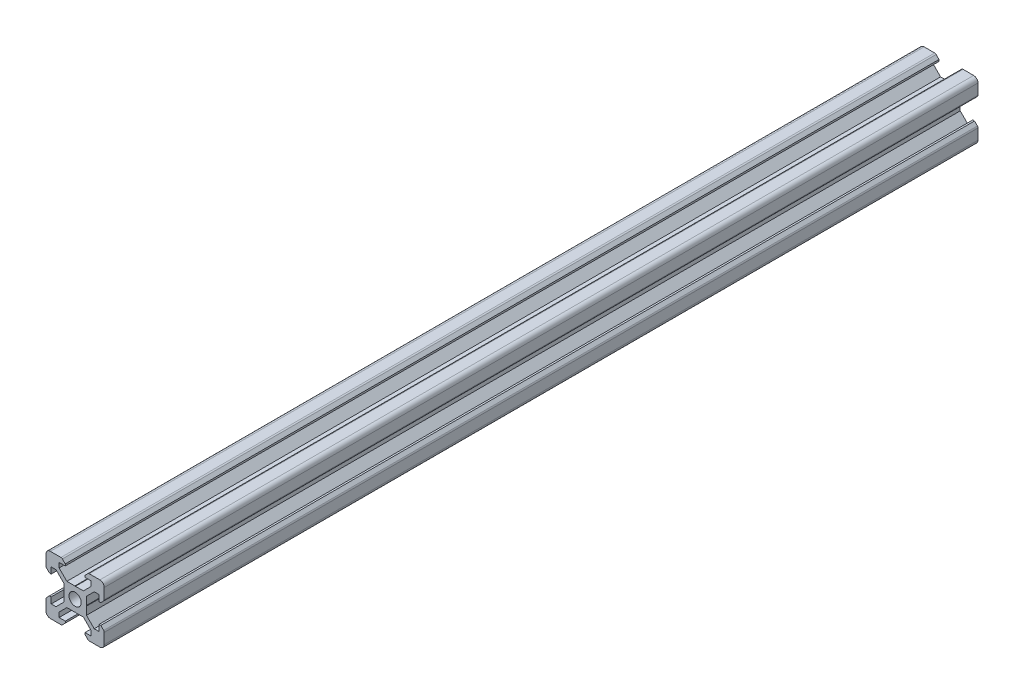
SolidWorks part; units mm, degrees
ref_plane "Front" through (0, 0, 0) normal (0, 0, 1) x (1, 0, 0)
ref_plane "Top" through (0, 0, 0) normal (0, 1, 0) x (1, 0, 0)
ref_plane "Right" through (0, 0, 0) normal (1, 0, 0) x (0, 0, -1)
sketch "Sketch1" plane through (0, 0, 0) normal (0, 0, 1) x (1, 0, 0)
  line L0 (-8.5, 10) -> (-10, 8.5) construction
  line L1 (-8.5, 10) -> (-4.8628, 10)
  line L2 (-10, 8.5) -> (-10, 4.8628)
  line L3 (-8.5, -10) -> (-4.8628, -10)
  line L4 (10, 8.5) -> (10, 4.8628)
  line L5 (-10, 10) -> (10, -10) construction
  line L6 (-10, -10) -> (10, 10) construction
  line L7 (-5.5, -8.2) -> (-3.3865, -8.2)
  line L8 (-8.2, -5.5) -> (-8.2, -3.3865)
  line L9 (-5.5, 8.2) -> (-3.3865, 8.2)
  line L10 (8.2, -5.5) -> (8.2, -3.3865)
  line L11 (-3.9005, 2.8395) -> (-6.561, 5.5)
  line L12 (-6.561, 5.5) -> (-8.2, 5.5)
  line L13 (-2.8395, -3.9005) -> (-0.1, -3.9005)
  line L14 (-3.9005, -2.8395) -> (-3.9005, -0.1)
  line L15 (-2.8395, 3.9005) -> (-0.1, 3.9005)
  line L16 (3.9005, -2.8395) -> (3.9005, -0.1)
  line L17 (-8.2, 3.3865) -> (-8.81, 3.3865)
  line L18 (-8.81, 3.3865) -> (-9.7976, 4.3741)
  line L19 (8.5, 10) -> (10, 8.5) construction
  line L20 (-2.8395, 3.9005) -> (-5.5, 6.561)
  line L21 (-5.5, 6.561) -> (-5.5, 8.2)
  line L22 (-3.3865, 8.2) -> (-3.3865, 8.81)
  line L23 (-3.3865, 8.81) -> (-4.3741, 9.7976)
  line L24 (0, 24.069) -> (0, -33.8154) construction
  line L25 (3.3865, 8.81) -> (4.3741, 9.7976)
  line L26 (3.3865, 8.2) -> (3.3865, 8.81)
  line L27 (5.5, 6.561) -> (5.5, 8.2)
  line L28 (2.8395, 3.9005) -> (5.5, 6.561)
  line L29 (3.3865, 8.2) -> (5.5, 8.2)
  line L30 (4.8628, 10) -> (8.5, 10)
  line L31 (-0.1, 3.9005) -> (0, 3.8005)
  line L32 (0.1, 3.9005) -> (0, 3.8005)
  line L33 (0.1, 3.9005) -> (2.8395, 3.9005)
  line L34 (25.9287, 0) -> (-28.3459, 0) construction
  line L35 (-0.1, -3.9005) -> (0, -3.8005)
  line L36 (0.1, -3.9005) -> (0, -3.8005)
  line L37 (0.1, -3.9005) -> (2.8395, -3.9005)
  line L38 (-3.9005, 0.1) -> (-3.8005, 0)
  line L39 (-3.8005, 0) -> (-3.9005, -0.1)
  line L40 (-3.9005, 0.1) -> (-3.9005, 2.8395)
  line L41 (3.9005, 0.1) -> (3.8005, 0)
  line L42 (3.8005, 0) -> (3.9005, -0.1)
  line L43 (3.9005, 0.1) -> (3.9005, 2.8395)
  line L44 (8.81, 3.3865) -> (9.7976, 4.3741)
  line L45 (8.2, 3.3865) -> (8.81, 3.3865)
  line L46 (6.561, 5.5) -> (8.2, 5.5)
  line L47 (3.9005, 2.8395) -> (6.561, 5.5)
  line L48 (2.8395, -3.9005) -> (5.5, -6.561)
  line L49 (3.9005, -2.8395) -> (6.561, -5.5)
  line L50 (-2.8395, -3.9005) -> (-5.5, -6.561)
  line L51 (-3.9005, -2.8395) -> (-6.561, -5.5)
  line L52 (6.561, -5.5) -> (8.2, -5.5)
  line L53 (-6.561, -5.5) -> (-8.2, -5.5)
  line L54 (-8.81, -3.3865) -> (-9.7976, -4.3741)
  line L55 (-8.2, -3.3865) -> (-8.81, -3.3865)
  line L56 (8.81, -3.3865) -> (9.7976, -4.3741)
  line L57 (8.2, -3.3865) -> (8.81, -3.3865)
  line L58 (8.2, 3.3865) -> (8.2, 5.5)
  line L59 (10, -4.8628) -> (10, -8.5)
  line L60 (-8.2, 3.3865) -> (-8.2, 5.5)
  line L61 (-10, -4.8628) -> (-10, -8.5)
  line L62 (-3.3865, -8.81) -> (-4.3741, -9.7976)
  line L63 (-3.3865, -8.2) -> (-3.3865, -8.81)
  line L64 (3.3865, -8.81) -> (4.3741, -9.7976)
  line L65 (3.3865, -8.2) -> (3.3865, -8.81)
  line L66 (-5.5, -6.561) -> (-5.5, -8.2)
  line L67 (5.5, -6.561) -> (5.5, -8.2)
  line L68 (3.3865, -8.2) -> (5.5, -8.2)
  line L69 (4.8628, -10) -> (8.5, -10)
  circle A0 centre (0, 0) radius 2.1
  arc A1 (-8.5, 10) -> (-10, 8.5) centre (-8.5, 8.5) ccw
  arc A2 (10, 8.5) -> (8.5, 10) centre (8.5, 8.5) ccw
  arc A3 (-4.3741, 9.7976) -> (-4.8628, 10) centre (-4.8628, 9.3088) ccw
  arc A4 (4.8628, 10) -> (4.3741, 9.7976) centre (4.8628, 9.3088) ccw
  arc A5 (-8.5, -10) -> (-10, -8.5) centre (-8.5, -8.5) cw
  arc A6 (9.7976, 4.3741) -> (10, 4.8628) centre (9.3088, 4.8628) ccw
  arc A7 (-10, 4.8628) -> (-9.7976, 4.3741) centre (-9.3088, 4.8628) ccw
  arc A8 (-10, -4.8628) -> (-9.7976, -4.3741) centre (-9.3088, -4.8628) cw
  arc A9 (9.7976, -4.3741) -> (10, -4.8628) centre (9.3088, -4.8628) cw
  arc A10 (10, -8.5) -> (8.5, -10) centre (8.5, -8.5) cw
  arc A11 (-4.3741, -9.7976) -> (-4.8628, -10) centre (-4.8628, -9.3088) cw
  arc A12 (4.8628, -10) -> (4.3741, -9.7976) centre (4.8628, -9.3088) cw
  point P17 (-9.25, 9.25)
  point P21 (9.25, 9.25)
  dimension "D2" = 4.2
  dimension "D4" = 1.5
  dimension "D3" = 20
  dimension "D5" = 0.529
  dimension "D6" = 6.773
  dimension "D7" = 90
  dimension "D8" = 11
  dimension "D9" = 0.61
  dimension "D10" = 0.1
  dimension "D11" = 0.1
  dimension "D12" = 0.1
  dimension "D13" = 0.1
  dimension "D14" = 5.679
  dimension "D15" = 1.639
  dimension "D16" = 1.8
  dimension "D17" = 90
  dimension "D18" = 6.773
  dimension "D19" = 90
extrude "Boss-Extrude1" add sketch "Sketch1" along normal blind 300
